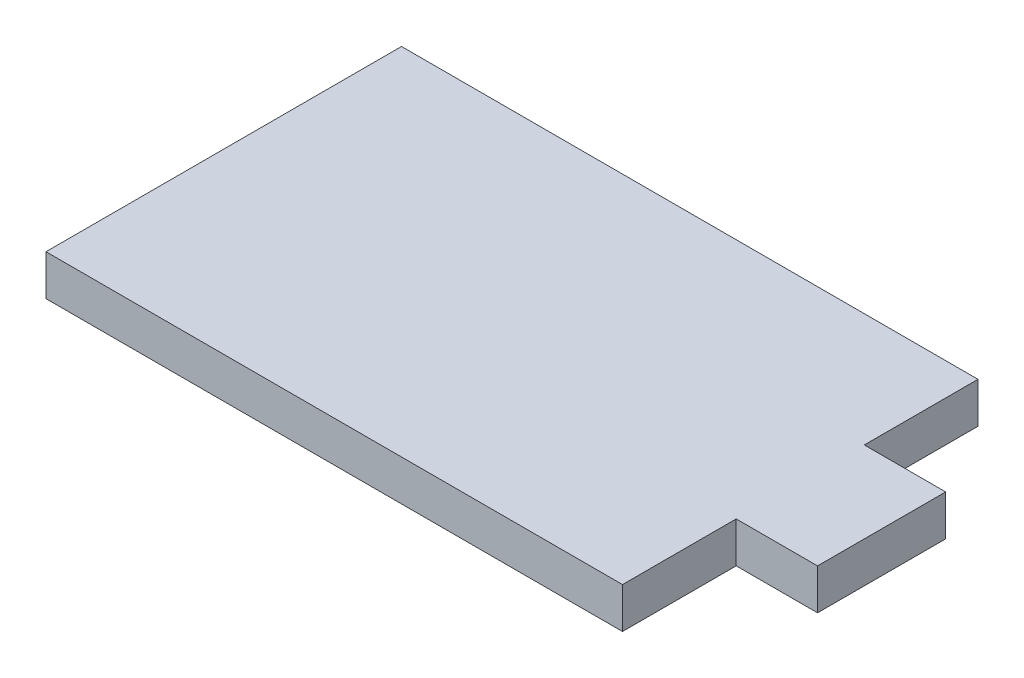
SolidWorks part; units mm, degrees
material "Cedar"
ref_plane "Front Plane" through (0, 0, 0) normal (0, 0, 1) x (1, 0, 0)
ref_plane "Top Plane" through (0, 0, 0) normal (0, 1, 0) x (1, 0, 0)
ref_plane "Right Plane" through (0, 0, 0) normal (1, 0, 0) x (0, 0, -1)
sketch "Sketch1" plane through (0, 0, 0) normal (0, 1, 0) x (1, 0, 0)
  line L0 (-22.5, 8.875) -> (22.5, 8.875)
  line L1 (22.5, 8.875) -> (22.5, 0)
  line L2 (22.5, 0) -> (28.85, 0)
  line L3 (28.85, 0) -> (28.85, -10)
  line L4 (28.85, -10) -> (22.5, -10)
  line L5 (22.5, -10) -> (22.5, -18.875)
  line L6 (22.5, -18.875) -> (-22.5, -18.875)
  line L7 (-22.5, -18.875) -> (-22.5, -10)
  line L8 (-22.5, -10) -> (-28.85, -10)
  line L9 (-28.85, -10) -> (-28.85, 0)
  line L10 (-28.85, 0) -> (-22.5, 0)
  line L11 (-22.5, 0) -> (-22.5, 8.875)
  line L12 (-22.5, 0) -> (-22.5, -10) construction
  point P11 (0, 8.875)
  point P14 (-28.85, -5)
  dimension "D1" = 6.35
  dimension "D2" = 10
  dimension "D3" = 45
  dimension "D4" = 27.75
extrude "Boss-Extrude1" add sketch "Sketch1" along normal blind 3.175 contours L11 L12 L7 L6 L5 L4 L3 L2 L1 L0
equation "\"length\"= 27.75mm"
equation "\"w_mach\"= 45mm"
equation "\"w_tab\"= 10mm"
equation "\"t_wood\"= 0.125in"
equation "\"t_side\"= 0.25in"
equation "\"D1@Sketch1\"=\"t_side\""
equation "\"D2@Sketch1\"=\"w_tab\""
equation "\"D3@Sketch1\"=\"w_mach\""
equation "\"D4@Sketch1\"=\"length\""
equation "\"D1@Boss-Extrude1\"=\"t_wood\""
